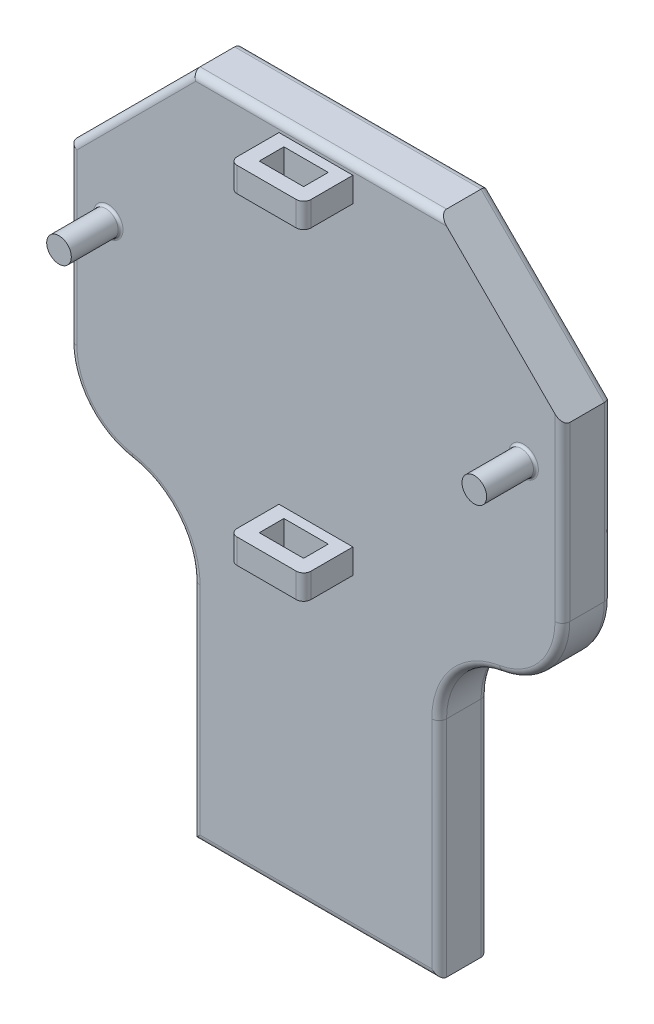
SolidWorks part; units mm, degrees
material "AISI Type 316L stainless steel"
ref_plane "Front Plane" through (0, 0, 0) normal (0, 0, 1) x (1, 0, 0)
ref_plane "Top Plane" through (0, 0, 0) normal (0, 1, 0) x (1, 0, 0)
ref_plane "Right Plane" through (0, 0, 0) normal (1, 0, 0) x (0, 0, -1)
sketch "Sketch1" plane through (0, 0, 0) normal (0, 0, 1) x (1, 0, 0)
  line L0 (-100, 0) -> (-50, 50)
  line L1 (-50, 50) -> (50, 50)
  line L2 (-100, 0) -> (-100, -50)
  line L3 (-100, -50) -> (100, -50)
  line L4 (100, 0) -> (100, -50)
  line L5 (-100, 50) -> (100, -50) construction
  line L6 (-100, -50) -> (100, 50) construction
  line L7 (50, 50) -> (100, 0)
  point P0 (0, 0)
  dimension "D1" = 100
  dimension "D2" = 200
extrude "Boss-Extrude1" add sketch "Sketch1" along normal blind 20
sketch "Sketch2" plane through (0, 0, 20) normal (0, 0, 1) x (1, 0, 0)
  line L0 (-100, -50) -> (100, -50) construction
  line L1 (-100, 0) -> (-100, -50) construction
  line L2 (0, 43.6708) -> (0, -37.1258) construction
  circle A0 centre (-84.27, -20) radius 5
  circle A1 centre (84.27, -20) radius 5
  dimension "D1" = 10
  dimension "D2" = 30
  dimension "D3" = 15.73
extrude "Boss-Extrude2" add sketch "Sketch2" along normal blind 20
sketch "Sketch3" plane through (0, -50, 0) normal (0, -1, 0) x (1, 0, 0)
  line L4 (-100, 0) -> (100, 0)
  line L5 (100, 0) -> (100, 20)
  line L6 (100, 20) -> (-100, 20)
  line L7 (-100, 20) -> (-100, 0)
  line L8 (-100, 0) -> (100, 0)
  line L9 (100, 0) -> (100, 20)
  line L10 (100, 20) -> (-100, 20)
  line L11 (-100, 20) -> (-100, 0)
  dimension "D1" = 0
extrude "Boss-Extrude3" add sketch "Sketch3" along normal blind 50
sketch "Sketch4" plane through (0, 0, 20) normal (0, 0, 1) x (1, 0, 0)
  line L0 (0, 30.5872) -> (0, -79.4696) construction
  line L1 (100, -100) -> (-100, -100) construction
  line L2 (-15, -84.75) -> (15, -84.75)
  line L3 (-15, -84.75) -> (-15, -94.75)
  line L4 (-15, -94.75) -> (15, -94.75)
  line L5 (15, -84.75) -> (15, -94.75)
  line L6 (-15, -84.75) -> (15, -94.75) construction
  line L7 (-15, -94.75) -> (15, -84.75) construction
  line L8 (0, 50) -> (0, -100) construction
  line L9 (50, 50) -> (-50, 50) construction
  line L10 (0, -24.4412) -> (77.6009, -24.4412) construction
  line L11 (-15, 45.8677) -> (15, 45.8677)
  line L12 (15, 35.8677) -> (15, 45.8677)
  line L13 (-15, 35.8677) -> (15, 35.8677)
  line L14 (-15, 35.8677) -> (-15, 45.8677)
  point P3 (0, -89.75)
  point P17 (0, -24.4412)
  dimension "D1" = 30
  dimension "D2" = 10
  dimension "D3" = 5.25
extrude "Boss-Extrude4" add sketch "Sketch4" along normal blind 20
sketch "Sketch5" plane through (0, -94.75, 0) normal (0, -1, 0) x (1, 0, 0)
  line L0 (100, 20) -> (-100, 20) construction
  line L4 (-9, 34) -> (9, 34)
  line L5 (-9, 34) -> (-9, 24)
  line L6 (-9, 24) -> (9, 24)
  line L7 (9, 34) -> (9, 24)
  line L8 (-9, 34) -> (9, 24) construction
  line L9 (-9, 24) -> (9, 34) construction
  point P6 (0, 29)
  dimension "D1" = 18
  dimension "D2" = 10
  dimension "D3" = 4
extrude "Cut-Extrude1" cut sketch "Sketch5" against normal through all
sketch "Sketch6" plane through (0, -100, 0) normal (0, -1, 0) x (1, 0, 0)
  line L0 (0, 20) -> (0, 0)
  line L1 (100, 20) -> (-100, 20) construction
  line L2 (0, 0) -> (-50, 0)
  line L3 (-50, 0) -> (-50, 20)
  line L4 (-50, 20) -> (0, 20)
  line L5 (0, 20) -> (50, 20)
  line L6 (50, 20) -> (50, 0)
  line L7 (50, 0) -> (0, 0)
  line M2 (-100, 0) -> (100, 0)
  line M4 (100, 20) -> (-100, 20)
extrude "Boss-Extrude5" add sketch "Sketch6" along normal blind 120 contours L3 L0 M2 M4 | L6 L0 M4 M2
fillet "Fillet1" radius 30 2 edges at (-100, -100, 10) (100, -100, 10)
fillet "Fillet2" radius 30 2 edges at (-50, -100, 10) (50, -100, 10)
fillet "Fillet3" radius 3 27 edges at (50, -174.5804, 20) (100, -35, 20) (100, -35, 0) (92.9129, -89.3649, 20) (92.9129, -89.3649, 0) (-100, -35, 0) (-100, -35, 20) (-92.9129, -89.3649, 0) (-92.9129, -89.3649, 20) (-57.0871, -109.7959, 0) (-57.0871, -109.7959, 20) (0, -220, 0) (50, -174.5804, 0) (57.0871, -109.7959, 20) (57.0871, -109.7959, 0) (75, 25, 0) (0, 50, 0) (0, 50, 20) (-75, 25, 0) (-75, 25, 20) (-50, -174.5804, 0) (0, -220, 20) (-50, -174.5804, 20) (15, 40.8677, 40) (-15, 40.8677, 40) (-15, -89.75, 40) (15, -89.75, 40)
fillet "Fillet4" radius 1 2 edges at (79.27, -20, 20) (-79.27, -20, 20)
